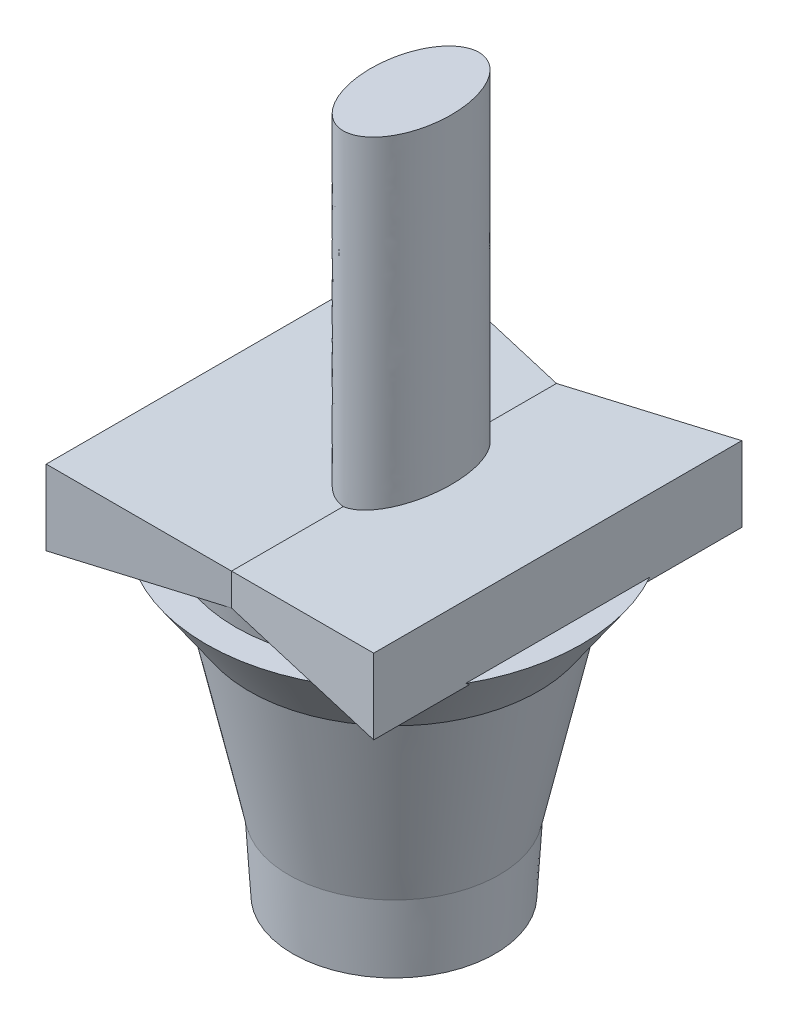
SolidWorks part; units mm, degrees
ref_plane "Alzado" through (0, 0, 0) normal (0, 0, 1) x (1, 0, 0)
ref_plane "Planta" through (0, 0, 0) normal (0, 1, 0) x (1, 0, 0)
ref_plane "Vista lateral" through (0, 0, 0) normal (1, 0, 0) x (0, 0, -1)
sketch "Croquis1" plane through (0, 0, 0) normal (1, 0, 0) x (0, 0, -1)
  line L0 (-15.6029, 61.2135) -> (-17.6029, 61.2135)
  line L1 (-8.2185, -13.6112) -> (-12.608, 61.3888)
  line L2 (-12.608, 61.3888) -> (-12.635, 0.0117) construction
  line L3 (-11.2134, -13.7865) -> (-15.6029, 61.2135)
  line L4 (-12.608, 61.3888) -> (-10.608, 61.3888)
  line L6 (-8.2185, -13.6112) -> (-6.2185, -13.6112)
  line L8 (-10.608, 61.3888) -> (-6.2185, -13.6112)
  line L9 (-11.2134, -13.7865) -> (-13.2134, -13.7865)
  line L10 (-17.6029, 61.2135) -> (-13.2134, -13.7865)
  line L11 (-22.5929, 61.2135) -> (-18.2034, -13.7865)
  line L12 (-16.2034, -13.7865) -> (-18.2034, -13.7865)
  line L13 (-16.2034, -13.7865) -> (-20.5929, 61.2135)
  line L14 (-20.5929, 61.2135) -> (-22.5929, 61.2135)
  line L15 (-27.5829, 61.2135) -> (-23.1934, -13.7865)
  line L16 (-21.1934, -13.7865) -> (-23.1934, -13.7865)
  line L17 (-21.1934, -13.7865) -> (-25.5829, 61.2135)
  line L18 (-25.5829, 61.2135) -> (-27.5829, 61.2135)
  line L19 (-29.1645, 2.9771) -> (-28.1834, -13.7865)
  line L20 (-26.1834, -13.7865) -> (-28.1834, -13.7865)
  line L21 (-26.1834, -13.7865) -> (-30.5729, 61.2135)
  line L23 (-29.1645, 2.9771) -> (-42.7789, 64.8462)
  line L24 (-42.7789, 64.8462) -> (-30.5729, 65.2135)
  line L25 (-30.5729, 65.2135) -> (-30.5729, 61.2135)
  line L27 (-30.5729, 61.2135) -> (-32.5729, 61.2135) [skipped]
  line L28 (-4.0946, 0.97) -> (-4.0946, 13.3366) construction
  point P3 (-16.6029, 61.2135)
  point P10 (-11.608, 61.3888)
  point P21 (0, 0)
  point P25 (0, 0)
  dimension "D8" = 79
  dimension "D2" = 2
  dimension "D4" = 2
  dimension "D5" = 2
  dimension "D3" = 2
  dimension "D6" = 4.9949
  dimension "D9" = 75
  dimension "D1" = 3
  dimension "D7" = 4
revolve "Revolución1" add sketch "Croquis1" angle 360 about L28
sketch "Croquis2" plane through (0, 0, 0) normal (0, 1, 0) x (1, 0, 0)
  circle A0 centre (0, -4.0946) radius 1.7829
extrude "Saliente-Extruir1" add sketch "Croquis2" along normal blind 2 separate body
ref_plane "Plano1" through (0, 62, 0) normal (0, -1, 0) x (-1, 0, 0)
sketch "Croquis3" plane through (0, 62, 0) normal (0, -1, 0) x (-1, 0, 0)
  circle A0 centre (0, -4.0946) radius 4.1365
loft "Recubrir1" add profiles "Croquis3" section edge at (0, 2, 5.8776) section "Croquis3"
sketch "Croquis5" plane through (0, 0, 0) normal (1, 0, 0) x (0, 0, -1)
  line L1 (-42.7789, 64.8462) -> (34.6312, 64.8462)
  line L2 (-42.7789, 64.8462) -> (-42.7789, 72.474)
  line L3 (-42.7789, 72.474) -> (34.6312, 72.474)
  line L4 (34.6312, 64.8462) -> (34.6312, 72.474)
extrude "Saliente-Extruir2" add sketch "Croquis5" along normal blind 39 draft 7.5 and the other way blind 39 draft 7.5 other way draft outward yes draft outward yes
ref_plane "Plano2" through (0, 150, 0) normal (0, 1, 0) x (1, 0, 0)
sketch "Croquis7" plane through (0, 150, 0) normal (0, 1, 0) x (1, 0, 0)
  line L0 (0, 34.6312) -> (0, -42.7789) construction
  ellipse E0 centre (0, 0) end of major axis (0, -16.1732) minor radius 9.5936
extrude "Saliente-Extruir3" add sketch "Croquis7" against normal blind 78
sketch "Croquis8" plane through (0, 0, 0) normal (1, 0, 0) x (0, 0, -1)
  line L2 (-4.0946, -13.7865) -> (-4.0946, 23.6102) construction
  line L3 (-28.1834, -13.7865) -> (19.9941, -13.7865) construction
  line L7 (-41.8027, 60.4099) -> (-48.8365, 60.4099)
  line L8 (-42.7789, 64.8462) -> (-29.1645, 2.9771) construction
  line L9 (-48.8365, 60.4099) -> (-38.5306, 45.5406)
  line L10 (-38.5306, 45.5406) -> (-41.8027, 60.4099)
revolve "Revolución4" add sketch "Croquis8" angle 360 about L2
sketch "Croquis9" plane through (0, -13.6112, 0) normal (0, -1, 0) x (1, 0, 0)
sketch "Croquis10" plane through (0, 62, 0) normal (0, -1, 0) x (-1, 0, 0)
sketch "Croquis11" plane through (0, 62, 0) normal (0, -1, 0) x (-1, 0, 0)
